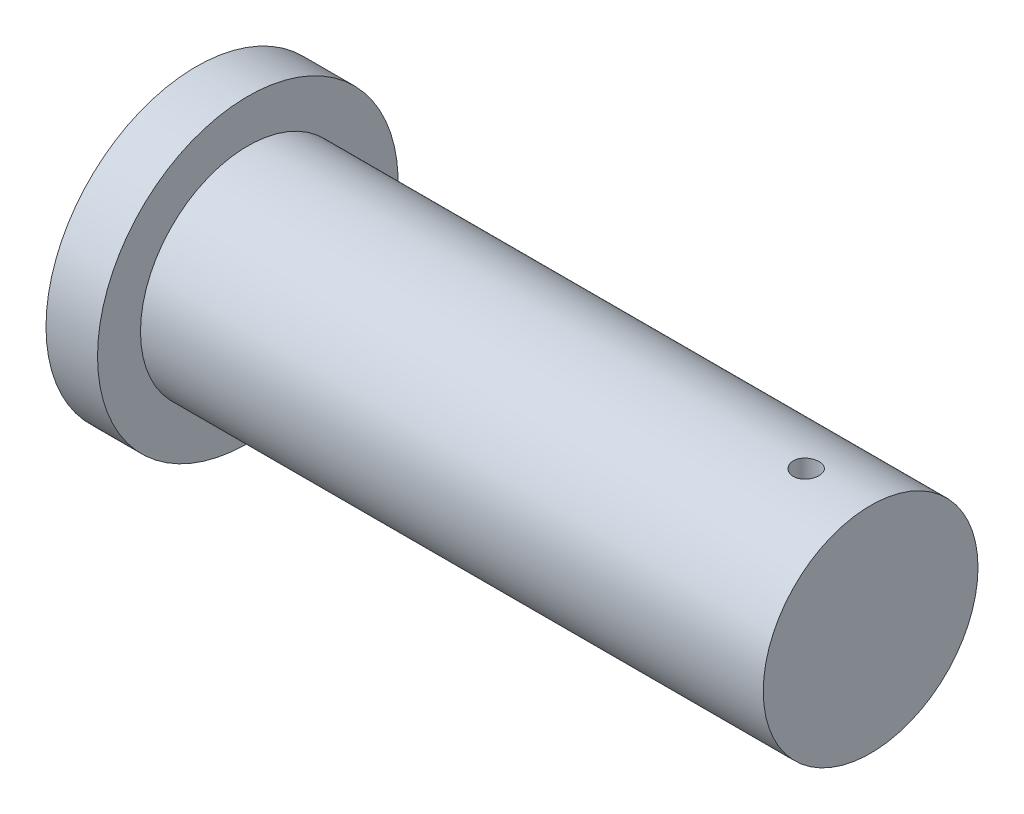
SolidWorks part; units mm, degrees
ref_plane "Front Plane" through (0, 0, 0) normal (0, 0, 1) x (1, 0, 0)
ref_plane "Top Plane" through (0, 0, 0) normal (0, 1, 0) x (1, 0, 0)
ref_plane "Right Plane" through (0, 0, 0) normal (1, 0, 0) x (0, 0, -1)
sketch "Sketch2" plane through (0, 0, 0) normal (0, 0, 1) x (1, 0, 0)
  line L0 (0, 0) -> (0, 250)
  line L1 (0, 250) -> (-1450, 250)
  line L2 (-1450, 250) -> (-1450, 350)
  line L3 (-1450, 350) -> (-1570, 350)
  line L4 (-1570, 350) -> (-1570, 0)
  line L5 (-1570, 0) -> (0, 0)
  dimension "D1" = 1570
  dimension "D2" = 350
  dimension "D3" = 120
  dimension "D4" = 250
revolve "Revolve1" add sketch "Sketch2" angle 360 about L5
sketch "Sketch3" plane through (0, 0, 0) normal (0, 1, 0) x (1, 0, 0)
  line L0 (-1450, -250) -> (-1450, 250) construction
  circle A0 centre (-150, 0) radius 30
  point P2 (0, 0)
  dimension "D1" = 60
  dimension "D2" = 1300
extrude "Cut-Extrude1" cut sketch "Sketch3" against normal through all both and the other way through all
